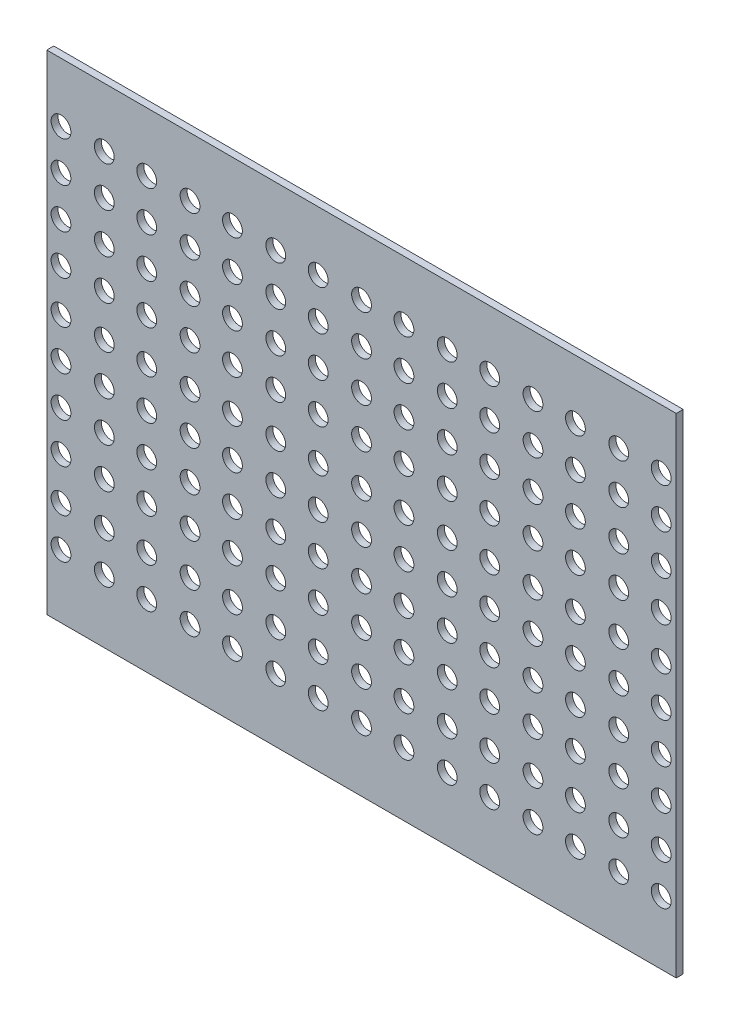
SolidWorks part; units mm, degrees
material "PVC Rigid"
ref_plane "Front" through (0, 0, 0) normal (0, 0, 1) x (1, 0, 0)
ref_plane "Top" through (0, 0, 0) normal (0, 1, 0) x (1, 0, 0)
ref_plane "Right" through (0, 0, 0) normal (1, 0, 0) x (0, 0, -1)
sketch "Sketch1" plane through (0, 0, 0) normal (0, 0, 1) x (1, 0, 0)
  line L0 (-26.15, -197) -> (-26.15, -206.525)
  line L1 (-26.15, -197) -> (260.15, -197) construction
  line L2 (-26.15, -197) -> (-26.15, 15.875)
  line L3 (-26.15, 15.875) -> (260.15, 15.875)
  line L5 (-4.5826, -197) -> (-14.7174, -197) construction
  line L6 (260.15, 15.875) -> (260.15, -197)
  line L7 (253.3, 0) -> (253.3, -6.4174) construction
  line L8 (214.7, 0) -> (253.3, 0) construction
  line L9 (-26.15, -206.525) -> (260.15, -206.525)
  line L12 (-19.3, -6.4174) -> (-19.3, 0) construction
  line L13 (260.15, -206.525) -> (260.15, -197)
  dimension "D2" = 15.875
  dimension "D4" = 6.85
  dimension "D5" = 6.85
  dimension "D1" = 9.525
extrude "Boss-Extrude1" add sketch "Sketch1" along normal blind 3.175
sketch "Sketch2" plane through (0, 0, 3.175) normal (0, 0, 1) x (1, 0, 0)
  line L0 (234, 11.561) -> (234, -33.561) construction
  line L1 (234, -11) -> (253.3, -11) construction
  line L2 (234, -85.2) -> (253.3, -85.2) construction
  line L3 (234, -159.4) -> (253.3, -159.4) construction
  circle A0 centre (253.3, -11) radius 4.5
  circle A1 centre (234, -11) radius 4.5
  circle A3 centre (253.3, -85.2) radius 4.5
  circle A6 centre (234, -85.2) radius 4.5
  circle A7 centre (253.3, -29.3) radius 4.5
  circle A10 centre (234, -29.3) radius 4.5
  circle A14 centre (253.3, -47.6) radius 4.5
  circle A15 centre (234, -47.6) radius 4.5
  circle A19 centre (253.3, -65.9) radius 4.5
  circle A22 centre (234, -65.9) radius 4.5
  arc A34 (199, -11) -> (191, -11) centre (195, -11) ccw
  arc A35 (191, -11) -> (199, -11) centre (195, -11) ccw
  arc A36 (199, -11) -> (191, -11) centre (195, -11) ccw construction
  circle A50 centre (253.3, -103.5) radius 4.5
  circle A51 centre (234, -103.5) radius 4.5
  circle A52 centre (253.3, -121.8) radius 4.5
  circle A53 centre (234, -121.8) radius 4.5
  circle A54 centre (253.3, -140.1) radius 4.5
  circle A55 centre (234, -140.1) radius 4.5
  circle A56 centre (253.3, -159.4) radius 4.5
  circle A57 centre (234, -159.4) radius 4.5
  circle A58 centre (253.3, -177.7) radius 4.5
  circle A59 centre (234, -177.7) radius 4.5
  circle A66 centre (253.3, -196) radius 4.5 [skipped]
  circle A67 centre (234, -196) radius 4.5 [skipped]
  circle A68 centre (253.3, -214.3) radius 4.5 [skipped]
  circle A69 centre (234, -214.3) radius 4.5 [skipped]
  point P1 (253.3, -29.3)
  point P2 (234, -11)
  point P4 (253.3, -11)
  point P5 (253.3, -103.5)
  point P10 (253.3, -11)
  point P12 (234, -85.2)
  point P15 (253.3, -85.2)
  point P22 (253.3, -85.2)
  point P49 (253.3, -177.7)
  point P50 (234, -159.4)
  point P51 (253.3, -159.4)
  point P54 (253.3, -159.4)
  dimension "D1" = 9
  dimension "D3" = 18.3
  dimension "D5" = 74.2
  dimension "D2" = 4
  dimension "D4" = 3
  dimension "D9" = 0
extrude "Cut-Extrude1" cut sketch "Sketch2" against normal up to surface (3.175 mm away) up to face at (117, -95.325, 0)
pattern_linear "LPattern1" count 8 spacing 39 along (-1, 0, 0) of "Cut-Extrude1"
equation "\"D4@Sketch1\"=\"front and back thickenss@FS2-EN-ACC-A-0002-V1, BATTERY MODULES SEGMENT.Assembly\"+0.5mm"
equation "\"D5@Sketch1\"=\"front and back thickenss@FS2-EN-ACC-A-0002-V1, BATTERY MODULES SEGMENT.Assembly\"+0.5mm"
equation "\"D1@Sketch1\"=\"bottom thickness@FS2-EN-ACC-A-0002-V1, BATTERY MODULES SEGMENT.Assembly\""
equation "\"D3@LPattern1\"=\"cell to cell distance@FS2-EN-ACC-A-0002-V1, BATTERY MODULES SEGMENT.Assembly\""
